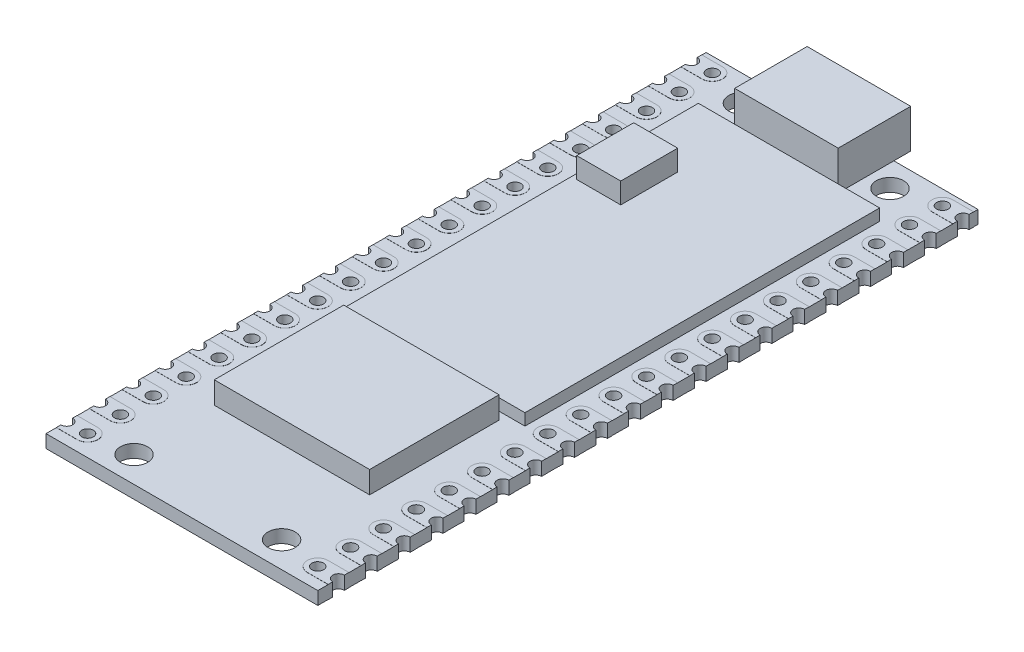
SolidWorks part; units mm, degrees
ref_plane "Front Plane" through (0, 0, 0) normal (0, 0, 1) x (1, 0, 0)
ref_plane "Top Plane" through (0, 0, 0) normal (0, 1, 0) x (1, 0, 0)
ref_plane "Right Plane" through (0, 0, 0) normal (1, 0, 0) x (0, 0, -1)
sketch "Sketch1" plane through (0, 0, 0) normal (0, 1, 0) x (1, 0, 0)
  line L0 (0, 0) -> (0, -51) construction
  line L1 (-10.5, 0) -> (10.5, 0)
  line L2 (-10.5, 0) -> (-10.5, -0.69)
  line L3 (-10.5, -51) -> (10.5, -51)
  line L4 (10.5, 0) -> (10.5, -0.69)
  line L5 (0, -25.5) -> (-10.5, -25.5) construction
  line L6 (-10.5, -48.95) -> (-8.89, -48.95) construction
  line L7 (-10.5, -49.85) -> (-10.5, -51)
  line L8 (10.5, -49.85) -> (10.5, -51)
  line L9 (-10.5, -47.31) -> (-10.5, -48.95)
  line L10 (-10.5, -44.77) -> (-10.5, -46.41)
  line L11 (-10.5, -42.23) -> (-10.5, -43.87)
  line L12 (-10.5, -39.69) -> (-10.5, -41.33)
  line L13 (-10.5, -37.15) -> (-10.5, -38.79)
  line L14 (-10.5, -34.61) -> (-10.5, -36.25)
  line L15 (-10.5, -32.07) -> (-10.5, -33.71)
  line L16 (-10.5, -29.53) -> (-10.5, -31.17)
  line L17 (-10.5, -26.99) -> (-10.5, -28.63)
  line L18 (-10.5, -24.45) -> (-10.5, -26.09)
  line L19 (-10.5, -21.91) -> (-10.5, -23.55)
  line L20 (-10.5, -19.37) -> (-10.5, -21.01)
  line L21 (-10.5, -16.83) -> (-10.5, -18.47)
  line L22 (-10.5, -14.29) -> (-10.5, -15.93)
  line L23 (-10.5, -11.75) -> (-10.5, -13.39)
  line L24 (-10.5, -9.21) -> (-10.5, -10.85)
  line L25 (-10.5, -6.67) -> (-10.5, -8.31)
  line L26 (-10.5, -4.13) -> (-10.5, -5.77)
  line L27 (-10.5, -1.59) -> (-10.5, -3.23)
  line L28 (10.5, -1.59) -> (10.5, -3.23)
  line L29 (10.5, -4.13) -> (10.5, -5.77)
  line L30 (10.5, -6.67) -> (10.5, -8.31)
  line L31 (10.5, -9.21) -> (10.5, -10.85)
  line L32 (10.5, -11.75) -> (10.5, -13.39)
  line L33 (10.5, -14.29) -> (10.5, -15.93)
  line L34 (10.5, -16.83) -> (10.5, -18.47)
  line L35 (10.5, -47.31) -> (10.5, -48.95)
  line L36 (10.5, -44.77) -> (10.5, -46.41)
  line L37 (10.5, -42.23) -> (10.5, -43.87)
  line L38 (10.5, -39.69) -> (10.5, -41.33)
  line L39 (10.5, -37.15) -> (10.5, -38.79)
  line L40 (10.5, -34.61) -> (10.5, -36.25)
  line L41 (10.5, -32.07) -> (10.5, -33.71)
  line L42 (10.5, -29.53) -> (10.5, -31.17)
  line L43 (10.5, -19.37) -> (10.5, -21.01)
  line L44 (10.5, -21.91) -> (10.5, -23.55)
  line L45 (10.5, -24.45) -> (10.5, -26.09)
  line L46 (10.5, -26.99) -> (10.5, -28.63)
  circle A0 centre (-5.7, -2) radius 1.05
  circle A1 centre (5.7, -2) radius 1.05
  circle A4 centre (-8.89, -49.4) radius 0.45
  arc A5 (-10.5, -49.85) -> (-10.5, -48.95) centre (-10.5, -49.4) ccw
  circle A6 centre (5.7, -49) radius 1.05
  circle A7 centre (-5.7, -49) radius 1.05
  arc A8 (10.5, -49.85) -> (10.5, -48.95) centre (10.5, -49.4) cw
  circle A9 centre (8.89, -49.4) radius 0.45
  arc A10 (-10.5, -47.31) -> (-10.5, -46.41) centre (-10.5, -46.86) ccw
  circle A11 centre (-8.89, -46.86) radius 0.45
  circle A12 centre (8.89, -46.86) radius 0.45
  arc A13 (10.5, -47.31) -> (10.5, -46.41) centre (10.5, -46.86) cw
  arc A14 (-10.5, -44.77) -> (-10.5, -43.87) centre (-10.5, -44.32) ccw
  circle A15 centre (-8.89, -44.32) radius 0.45
  circle A16 centre (8.89, -44.32) radius 0.45
  arc A17 (10.5, -44.77) -> (10.5, -43.87) centre (10.5, -44.32) cw
  arc A18 (-10.5, -42.23) -> (-10.5, -41.33) centre (-10.5, -41.78) ccw
  circle A19 centre (-8.89, -41.78) radius 0.45
  circle A20 centre (8.89, -41.78) radius 0.45
  arc A21 (10.5, -42.23) -> (10.5, -41.33) centre (10.5, -41.78) cw
  arc A22 (-10.5, -39.69) -> (-10.5, -38.79) centre (-10.5, -39.24) ccw
  circle A23 centre (-8.89, -39.24) radius 0.45
  circle A24 centre (8.89, -39.24) radius 0.45
  arc A25 (10.5, -39.69) -> (10.5, -38.79) centre (10.5, -39.24) cw
  arc A26 (-10.5, -37.15) -> (-10.5, -36.25) centre (-10.5, -36.7) ccw
  circle A27 centre (-8.89, -36.7) radius 0.45
  circle A28 centre (8.89, -36.7) radius 0.45
  arc A29 (10.5, -37.15) -> (10.5, -36.25) centre (10.5, -36.7) cw
  arc A30 (-10.5, -34.61) -> (-10.5, -33.71) centre (-10.5, -34.16) ccw
  circle A31 centre (-8.89, -34.16) radius 0.45
  circle A32 centre (8.89, -34.16) radius 0.45
  arc A33 (10.5, -34.61) -> (10.5, -33.71) centre (10.5, -34.16) cw
  arc A34 (-10.5, -32.07) -> (-10.5, -31.17) centre (-10.5, -31.62) ccw
  circle A35 centre (-8.89, -31.62) radius 0.45
  circle A36 centre (8.89, -31.62) radius 0.45
  arc A37 (10.5, -32.07) -> (10.5, -31.17) centre (10.5, -31.62) cw
  arc A38 (-10.5, -29.53) -> (-10.5, -28.63) centre (-10.5, -29.08) ccw
  circle A39 centre (-8.89, -29.08) radius 0.45
  circle A40 centre (8.89, -29.08) radius 0.45
  arc A41 (10.5, -29.53) -> (10.5, -28.63) centre (10.5, -29.08) cw
  arc A42 (-10.5, -26.99) -> (-10.5, -26.09) centre (-10.5, -26.54) ccw
  circle A43 centre (-8.89, -26.54) radius 0.45
  circle A44 centre (8.89, -26.54) radius 0.45
  arc A45 (10.5, -26.99) -> (10.5, -26.09) centre (10.5, -26.54) cw
  arc A46 (-10.5, -24.45) -> (-10.5, -23.55) centre (-10.5, -24) ccw
  circle A47 centre (-8.89, -24) radius 0.45
  circle A48 centre (8.89, -24) radius 0.45
  arc A49 (10.5, -24.45) -> (10.5, -23.55) centre (10.5, -24) cw
  arc A50 (-10.5, -21.91) -> (-10.5, -21.01) centre (-10.5, -21.46) ccw
  circle A51 centre (-8.89, -21.46) radius 0.45
  circle A52 centre (8.89, -21.46) radius 0.45
  arc A53 (10.5, -21.91) -> (10.5, -21.01) centre (10.5, -21.46) cw
  arc A54 (-10.5, -19.37) -> (-10.5, -18.47) centre (-10.5, -18.92) ccw
  circle A55 centre (-8.89, -18.92) radius 0.45
  circle A56 centre (8.89, -18.92) radius 0.45
  arc A57 (10.5, -19.37) -> (10.5, -18.47) centre (10.5, -18.92) cw
  arc A58 (-10.5, -16.83) -> (-10.5, -15.93) centre (-10.5, -16.38) ccw
  circle A59 centre (-8.89, -16.38) radius 0.45
  circle A60 centre (8.89, -16.38) radius 0.45
  arc A61 (10.5, -16.83) -> (10.5, -15.93) centre (10.5, -16.38) cw
  arc A62 (-10.5, -14.29) -> (-10.5, -13.39) centre (-10.5, -13.84) ccw
  circle A63 centre (-8.89, -13.84) radius 0.45
  circle A64 centre (8.89, -13.84) radius 0.45
  arc A65 (10.5, -14.29) -> (10.5, -13.39) centre (10.5, -13.84) cw
  arc A66 (-10.5, -11.75) -> (-10.5, -10.85) centre (-10.5, -11.3) ccw
  circle A67 centre (-8.89, -11.3) radius 0.45
  circle A68 centre (8.89, -11.3) radius 0.45
  arc A69 (10.5, -11.75) -> (10.5, -10.85) centre (10.5, -11.3) cw
  arc A70 (-10.5, -9.21) -> (-10.5, -8.31) centre (-10.5, -8.76) ccw
  circle A71 centre (-8.89, -8.76) radius 0.45
  circle A72 centre (8.89, -8.76) radius 0.45
  arc A73 (10.5, -9.21) -> (10.5, -8.31) centre (10.5, -8.76) cw
  arc A74 (-10.5, -6.67) -> (-10.5, -5.77) centre (-10.5, -6.22) ccw
  circle A75 centre (-8.89, -6.22) radius 0.45
  circle A76 centre (8.89, -6.22) radius 0.45
  arc A77 (10.5, -6.67) -> (10.5, -5.77) centre (10.5, -6.22) cw
  arc A78 (-10.5, -4.13) -> (-10.5, -3.23) centre (-10.5, -3.68) ccw
  circle A79 centre (-8.89, -3.68) radius 0.45
  circle A80 centre (8.89, -3.68) radius 0.45
  arc A81 (10.5, -4.13) -> (10.5, -3.23) centre (10.5, -3.68) cw
  arc A82 (-10.5, -1.59) -> (-10.5, -0.69) centre (-10.5, -1.14) ccw
  circle A83 centre (-8.89, -1.14) radius 0.45
  circle A84 centre (8.89, -1.14) radius 0.45
  arc A85 (10.5, -1.59) -> (10.5, -0.69) centre (10.5, -1.14) cw
other "Pen Sketch1" parameters "D3"=3.5614, "D8"=2.0664, "D1"=79.4088, "D2"=21, "D4"=15.5245, "D5"=11.4, "D6"=25.5, "D7"=1.5119, "D10"=2.54, "D9"=20
extrude "Boss-Extrude1" add sketch "Sketch1" along normal blind 1
sketch "Sketch2" plane through (0, 1, 0) normal (0, 1, 0) x (1, 0, 0)
  line L0 (0, -4.3) -> (0, 0) construction
  line L1 (-4, 1.3) -> (4, 1.3)
  line L2 (-4, 1.3) -> (-4, -4.3)
  line L3 (-4, -4.3) -> (4, -4.3)
  line L4 (4, 1.3) -> (4, -4.3)
  line L5 (10.5, 0) -> (-10.5, 0) construction
  dimension "D1" = 8
  dimension "D2" = 5.6
  dimension "D3" = 4.3
extrude "Boss-Extrude2" add sketch "Sketch2" along normal blind 3
sketch "Sketch3" plane through (0, 1, 0) normal (0, 1, 0) x (1, 0, 0)
  line L0 (-8.89, -48.6) -> (-10.5, -48.6)
  line L1 (-10.5, -47.31) -> (-10.5, -48.95) construction
  line L2 (-10.5, -48.6) -> (-10.5, -48.95)
  line L4 (-10.5, -49.85) -> (-10.5, -50.2)
  line L5 (-10.5, -49.85) -> (-10.5, -51) construction
  line L6 (-10.5, -50.2) -> (-8.89, -50.2)
  line L7 (0, 0) -> (0, -51) construction
  line L8 (-10.5, -51) -> (10.5, -51) construction
  line L9 (10.5, -50.2) -> (8.89, -50.2)
  line L10 (10.5, -49.85) -> (10.5, -50.2)
  line L11 (10.5, -48.6) -> (10.5, -48.95)
  line L12 (8.89, -48.6) -> (10.5, -48.6)
  line L13 (-8.89, -46.06) -> (-10.5, -46.06)
  line L14 (-10.5, -46.06) -> (-10.5, -46.41)
  line L15 (-10.5, -47.31) -> (-10.5, -47.66)
  line L16 (-10.5, -47.66) -> (-8.89, -47.66)
  line L17 (10.5, -47.66) -> (8.89, -47.66)
  line L18 (10.5, -47.31) -> (10.5, -47.66)
  line L19 (10.5, -46.06) -> (10.5, -46.41)
  line L20 (8.89, -46.06) -> (10.5, -46.06)
  line L21 (-8.89, -43.52) -> (-10.5, -43.52)
  line L22 (-10.5, -43.52) -> (-10.5, -43.87)
  line L23 (-10.5, -44.77) -> (-10.5, -45.12)
  line L24 (-10.5, -45.12) -> (-8.89, -45.12)
  line L25 (10.5, -45.12) -> (8.89, -45.12)
  line L26 (10.5, -44.77) -> (10.5, -45.12)
  line L27 (10.5, -43.52) -> (10.5, -43.87)
  line L28 (8.89, -43.52) -> (10.5, -43.52)
  line L29 (-8.89, -40.98) -> (-10.5, -40.98)
  line L30 (-10.5, -40.98) -> (-10.5, -41.33)
  line L31 (-10.5, -42.23) -> (-10.5, -42.58)
  line L32 (-10.5, -42.58) -> (-8.89, -42.58)
  line L33 (10.5, -42.58) -> (8.89, -42.58)
  line L34 (10.5, -42.23) -> (10.5, -42.58)
  line L35 (10.5, -40.98) -> (10.5, -41.33)
  line L36 (8.89, -40.98) -> (10.5, -40.98)
  line L37 (-8.89, -38.44) -> (-10.5, -38.44)
  line L38 (-10.5, -38.44) -> (-10.5, -38.79)
  line L39 (-10.5, -39.69) -> (-10.5, -40.04)
  line L40 (-10.5, -40.04) -> (-8.89, -40.04)
  line L41 (10.5, -40.04) -> (8.89, -40.04)
  line L42 (10.5, -39.69) -> (10.5, -40.04)
  line L43 (10.5, -38.44) -> (10.5, -38.79)
  line L44 (8.89, -38.44) -> (10.5, -38.44)
  line L45 (-8.89, -35.9) -> (-10.5, -35.9)
  line L46 (-10.5, -35.9) -> (-10.5, -36.25)
  line L47 (-10.5, -37.15) -> (-10.5, -37.5)
  line L48 (-10.5, -37.5) -> (-8.89, -37.5)
  line L49 (10.5, -37.5) -> (8.89, -37.5)
  line L50 (10.5, -37.15) -> (10.5, -37.5)
  line L51 (10.5, -35.9) -> (10.5, -36.25)
  line L52 (8.89, -35.9) -> (10.5, -35.9)
  line L53 (-8.89, -33.36) -> (-10.5, -33.36)
  line L54 (-10.5, -33.36) -> (-10.5, -33.71)
  line L55 (-10.5, -34.61) -> (-10.5, -34.96)
  line L56 (-10.5, -34.96) -> (-8.89, -34.96)
  line L57 (10.5, -34.96) -> (8.89, -34.96)
  line L58 (10.5, -34.61) -> (10.5, -34.96)
  line L59 (10.5, -33.36) -> (10.5, -33.71)
  line L60 (8.89, -33.36) -> (10.5, -33.36)
  line L61 (-8.89, -30.82) -> (-10.5, -30.82)
  line L62 (-10.5, -30.82) -> (-10.5, -31.17)
  line L63 (-10.5, -32.07) -> (-10.5, -32.42)
  line L64 (-10.5, -32.42) -> (-8.89, -32.42)
  line L65 (10.5, -32.42) -> (8.89, -32.42)
  line L66 (10.5, -32.07) -> (10.5, -32.42)
  line L67 (10.5, -30.82) -> (10.5, -31.17)
  line L68 (8.89, -30.82) -> (10.5, -30.82)
  line L69 (-8.89, -28.28) -> (-10.5, -28.28)
  line L70 (-10.5, -28.28) -> (-10.5, -28.63)
  line L71 (-10.5, -29.53) -> (-10.5, -29.88)
  line L72 (-10.5, -29.88) -> (-8.89, -29.88)
  line L73 (10.5, -29.88) -> (8.89, -29.88)
  line L74 (10.5, -29.53) -> (10.5, -29.88)
  line L75 (10.5, -28.28) -> (10.5, -28.63)
  line L76 (8.89, -28.28) -> (10.5, -28.28)
  line L77 (-8.89, -25.74) -> (-10.5, -25.74)
  line L78 (-10.5, -25.74) -> (-10.5, -26.09)
  line L79 (-10.5, -26.99) -> (-10.5, -27.34)
  line L80 (-10.5, -27.34) -> (-8.89, -27.34)
  line L81 (10.5, -27.34) -> (8.89, -27.34)
  line L82 (10.5, -26.99) -> (10.5, -27.34)
  line L83 (10.5, -25.74) -> (10.5, -26.09)
  line L84 (8.89, -25.74) -> (10.5, -25.74)
  line L85 (-8.89, -23.2) -> (-10.5, -23.2)
  line L86 (-10.5, -23.2) -> (-10.5, -23.55)
  line L87 (-10.5, -24.45) -> (-10.5, -24.8)
  line L88 (-10.5, -24.8) -> (-8.89, -24.8)
  line L89 (10.5, -24.8) -> (8.89, -24.8)
  line L90 (10.5, -24.45) -> (10.5, -24.8)
  line L91 (10.5, -23.2) -> (10.5, -23.55)
  line L92 (8.89, -23.2) -> (10.5, -23.2)
  line L93 (-8.89, -20.66) -> (-10.5, -20.66)
  line L94 (-10.5, -20.66) -> (-10.5, -21.01)
  line L95 (-10.5, -21.91) -> (-10.5, -22.26)
  line L96 (-10.5, -22.26) -> (-8.89, -22.26)
  line L97 (10.5, -22.26) -> (8.89, -22.26)
  line L98 (10.5, -21.91) -> (10.5, -22.26)
  line L99 (10.5, -20.66) -> (10.5, -21.01)
  line L100 (8.89, -20.66) -> (10.5, -20.66)
  line L101 (-8.89, -18.12) -> (-10.5, -18.12)
  line L102 (-10.5, -18.12) -> (-10.5, -18.47)
  line L103 (-10.5, -19.37) -> (-10.5, -19.72)
  line L104 (-10.5, -19.72) -> (-8.89, -19.72)
  line L105 (10.5, -19.72) -> (8.89, -19.72)
  line L106 (10.5, -19.37) -> (10.5, -19.72)
  line L107 (10.5, -18.12) -> (10.5, -18.47)
  line L108 (8.89, -18.12) -> (10.5, -18.12)
  line L109 (-8.89, -15.58) -> (-10.5, -15.58)
  line L110 (-10.5, -15.58) -> (-10.5, -15.93)
  line L111 (-10.5, -16.83) -> (-10.5, -17.18)
  line L112 (-10.5, -17.18) -> (-8.89, -17.18)
  line L113 (10.5, -17.18) -> (8.89, -17.18)
  line L114 (10.5, -16.83) -> (10.5, -17.18)
  line L115 (10.5, -15.58) -> (10.5, -15.93)
  line L116 (8.89, -15.58) -> (10.5, -15.58)
  line L117 (-8.89, -13.04) -> (-10.5, -13.04)
  line L118 (-10.5, -13.04) -> (-10.5, -13.39)
  line L119 (-10.5, -14.29) -> (-10.5, -14.64)
  line L120 (-10.5, -14.64) -> (-8.89, -14.64)
  line L121 (10.5, -14.64) -> (8.89, -14.64)
  line L122 (10.5, -14.29) -> (10.5, -14.64)
  line L123 (10.5, -13.04) -> (10.5, -13.39)
  line L124 (8.89, -13.04) -> (10.5, -13.04)
  line L125 (-8.89, -10.5) -> (-10.5, -10.5)
  line L126 (-10.5, -10.5) -> (-10.5, -10.85)
  line L127 (-10.5, -11.75) -> (-10.5, -12.1)
  line L128 (-10.5, -12.1) -> (-8.89, -12.1)
  line L129 (10.5, -12.1) -> (8.89, -12.1)
  line L130 (10.5, -11.75) -> (10.5, -12.1)
  line L131 (10.5, -10.5) -> (10.5, -10.85)
  line L132 (8.89, -10.5) -> (10.5, -10.5)
  line L133 (-8.89, -7.96) -> (-10.5, -7.96)
  line L134 (-10.5, -7.96) -> (-10.5, -8.31)
  line L135 (-10.5, -9.21) -> (-10.5, -9.56)
  line L136 (-10.5, -9.56) -> (-8.89, -9.56)
  line L137 (10.5, -9.56) -> (8.89, -9.56)
  line L138 (10.5, -9.21) -> (10.5, -9.56)
  line L139 (10.5, -7.96) -> (10.5, -8.31)
  line L140 (8.89, -7.96) -> (10.5, -7.96)
  line L141 (-8.89, -5.42) -> (-10.5, -5.42)
  line L142 (-10.5, -5.42) -> (-10.5, -5.77)
  line L143 (-10.5, -6.67) -> (-10.5, -7.02)
  line L144 (-10.5, -7.02) -> (-8.89, -7.02)
  line L145 (10.5, -7.02) -> (8.89, -7.02)
  line L146 (10.5, -6.67) -> (10.5, -7.02)
  line L147 (10.5, -5.42) -> (10.5, -5.77)
  line L148 (8.89, -5.42) -> (10.5, -5.42)
  line L149 (-8.89, -2.88) -> (-10.5, -2.88)
  line L150 (-10.5, -2.88) -> (-10.5, -3.23)
  line L151 (-10.5, -4.13) -> (-10.5, -4.48)
  line L152 (-10.5, -4.48) -> (-8.89, -4.48)
  line L153 (10.5, -4.48) -> (8.89, -4.48)
  line L154 (10.5, -4.13) -> (10.5, -4.48)
  line L155 (10.5, -2.88) -> (10.5, -3.23)
  line L156 (8.89, -2.88) -> (10.5, -2.88)
  line L157 (-8.89, -0.34) -> (-10.5, -0.34)
  line L158 (-10.5, -0.34) -> (-10.5, -0.69)
  line L159 (-10.5, -1.59) -> (-10.5, -1.94)
  line L160 (-10.5, -1.94) -> (-8.89, -1.94)
  line L161 (10.5, -1.94) -> (8.89, -1.94)
  line L162 (10.5, -1.59) -> (10.5, -1.94)
  line L163 (10.5, -0.34) -> (10.5, -0.69)
  line L164 (8.89, -0.34) -> (10.5, -0.34)
  arc A0 (-8.89, -50.2) -> (-8.89, -48.6) centre (-8.89, -49.4) ccw
  arc A1 (-10.5, -49.85) -> (-10.5, -48.95) centre (-10.5, -49.4) ccw
  circle A2 centre (-8.89, -49.4) radius 0.45
  circle A3 centre (-8.89, -49.4) radius 0.45 construction
  arc A4 (-10.5, -49.85) -> (-10.5, -48.95) centre (-10.5, -49.4) ccw construction
  circle A5 centre (8.89, -49.4) radius 0.45
  arc A6 (10.5, -49.85) -> (10.5, -48.95) centre (10.5, -49.4) cw
  arc A7 (8.89, -50.2) -> (8.89, -48.6) centre (8.89, -49.4) cw
  arc A8 (-8.89, -47.66) -> (-8.89, -46.06) centre (-8.89, -46.86) ccw
  arc A9 (-10.5, -47.31) -> (-10.5, -46.41) centre (-10.5, -46.86) ccw
  circle A10 centre (-8.89, -46.86) radius 0.45
  circle A11 centre (8.89, -46.86) radius 0.45
  arc A12 (10.5, -47.31) -> (10.5, -46.41) centre (10.5, -46.86) cw
  arc A13 (8.89, -47.66) -> (8.89, -46.06) centre (8.89, -46.86) cw
  arc A14 (-8.89, -45.12) -> (-8.89, -43.52) centre (-8.89, -44.32) ccw
  arc A15 (-10.5, -44.77) -> (-10.5, -43.87) centre (-10.5, -44.32) ccw
  circle A16 centre (-8.89, -44.32) radius 0.45
  circle A17 centre (8.89, -44.32) radius 0.45
  arc A18 (10.5, -44.77) -> (10.5, -43.87) centre (10.5, -44.32) cw
  arc A19 (8.89, -45.12) -> (8.89, -43.52) centre (8.89, -44.32) cw
  arc A20 (-8.89, -42.58) -> (-8.89, -40.98) centre (-8.89, -41.78) ccw
  arc A21 (-10.5, -42.23) -> (-10.5, -41.33) centre (-10.5, -41.78) ccw
  circle A22 centre (-8.89, -41.78) radius 0.45
  circle A23 centre (8.89, -41.78) radius 0.45
  arc A24 (10.5, -42.23) -> (10.5, -41.33) centre (10.5, -41.78) cw
  arc A25 (8.89, -42.58) -> (8.89, -40.98) centre (8.89, -41.78) cw
  arc A26 (-8.89, -40.04) -> (-8.89, -38.44) centre (-8.89, -39.24) ccw
  arc A27 (-10.5, -39.69) -> (-10.5, -38.79) centre (-10.5, -39.24) ccw
  circle A28 centre (-8.89, -39.24) radius 0.45
  circle A29 centre (8.89, -39.24) radius 0.45
  arc A30 (10.5, -39.69) -> (10.5, -38.79) centre (10.5, -39.24) cw
  arc A31 (8.89, -40.04) -> (8.89, -38.44) centre (8.89, -39.24) cw
  arc A32 (-8.89, -37.5) -> (-8.89, -35.9) centre (-8.89, -36.7) ccw
  arc A33 (-10.5, -37.15) -> (-10.5, -36.25) centre (-10.5, -36.7) ccw
  circle A34 centre (-8.89, -36.7) radius 0.45
  circle A35 centre (8.89, -36.7) radius 0.45
  arc A36 (10.5, -37.15) -> (10.5, -36.25) centre (10.5, -36.7) cw
  arc A37 (8.89, -37.5) -> (8.89, -35.9) centre (8.89, -36.7) cw
  arc A38 (-8.89, -34.96) -> (-8.89, -33.36) centre (-8.89, -34.16) ccw
  arc A39 (-10.5, -34.61) -> (-10.5, -33.71) centre (-10.5, -34.16) ccw
  circle A40 centre (-8.89, -34.16) radius 0.45
  circle A41 centre (8.89, -34.16) radius 0.45
  arc A42 (10.5, -34.61) -> (10.5, -33.71) centre (10.5, -34.16) cw
  arc A43 (8.89, -34.96) -> (8.89, -33.36) centre (8.89, -34.16) cw
  arc A44 (-8.89, -32.42) -> (-8.89, -30.82) centre (-8.89, -31.62) ccw
  arc A45 (-10.5, -32.07) -> (-10.5, -31.17) centre (-10.5, -31.62) ccw
  circle A46 centre (-8.89, -31.62) radius 0.45
  circle A47 centre (8.89, -31.62) radius 0.45
  arc A48 (10.5, -32.07) -> (10.5, -31.17) centre (10.5, -31.62) cw
  arc A49 (8.89, -32.42) -> (8.89, -30.82) centre (8.89, -31.62) cw
  arc A50 (-8.89, -29.88) -> (-8.89, -28.28) centre (-8.89, -29.08) ccw
  arc A51 (-10.5, -29.53) -> (-10.5, -28.63) centre (-10.5, -29.08) ccw
  circle A52 centre (-8.89, -29.08) radius 0.45
  circle A53 centre (8.89, -29.08) radius 0.45
  arc A54 (10.5, -29.53) -> (10.5, -28.63) centre (10.5, -29.08) cw
  arc A55 (8.89, -29.88) -> (8.89, -28.28) centre (8.89, -29.08) cw
  arc A56 (-8.89, -27.34) -> (-8.89, -25.74) centre (-8.89, -26.54) ccw
  arc A57 (-10.5, -26.99) -> (-10.5, -26.09) centre (-10.5, -26.54) ccw
  circle A58 centre (-8.89, -26.54) radius 0.45
  circle A59 centre (8.89, -26.54) radius 0.45
  arc A60 (10.5, -26.99) -> (10.5, -26.09) centre (10.5, -26.54) cw
  arc A61 (8.89, -27.34) -> (8.89, -25.74) centre (8.89, -26.54) cw
  arc A62 (-8.89, -24.8) -> (-8.89, -23.2) centre (-8.89, -24) ccw
  arc A63 (-10.5, -24.45) -> (-10.5, -23.55) centre (-10.5, -24) ccw
  circle A64 centre (-8.89, -24) radius 0.45
  circle A65 centre (8.89, -24) radius 0.45
  arc A66 (10.5, -24.45) -> (10.5, -23.55) centre (10.5, -24) cw
  arc A67 (8.89, -24.8) -> (8.89, -23.2) centre (8.89, -24) cw
  arc A68 (-8.89, -22.26) -> (-8.89, -20.66) centre (-8.89, -21.46) ccw
  arc A69 (-10.5, -21.91) -> (-10.5, -21.01) centre (-10.5, -21.46) ccw
  circle A70 centre (-8.89, -21.46) radius 0.45
  circle A71 centre (8.89, -21.46) radius 0.45
  arc A72 (10.5, -21.91) -> (10.5, -21.01) centre (10.5, -21.46) cw
  arc A73 (8.89, -22.26) -> (8.89, -20.66) centre (8.89, -21.46) cw
  arc A74 (-8.89, -19.72) -> (-8.89, -18.12) centre (-8.89, -18.92) ccw
  arc A75 (-10.5, -19.37) -> (-10.5, -18.47) centre (-10.5, -18.92) ccw
  circle A76 centre (-8.89, -18.92) radius 0.45
  circle A77 centre (8.89, -18.92) radius 0.45
  arc A78 (10.5, -19.37) -> (10.5, -18.47) centre (10.5, -18.92) cw
  arc A79 (8.89, -19.72) -> (8.89, -18.12) centre (8.89, -18.92) cw
  arc A80 (-8.89, -17.18) -> (-8.89, -15.58) centre (-8.89, -16.38) ccw
  arc A81 (-10.5, -16.83) -> (-10.5, -15.93) centre (-10.5, -16.38) ccw
  circle A82 centre (-8.89, -16.38) radius 0.45
  circle A83 centre (8.89, -16.38) radius 0.45
  arc A84 (10.5, -16.83) -> (10.5, -15.93) centre (10.5, -16.38) cw
  arc A85 (8.89, -17.18) -> (8.89, -15.58) centre (8.89, -16.38) cw
  arc A86 (-8.89, -14.64) -> (-8.89, -13.04) centre (-8.89, -13.84) ccw
  arc A87 (-10.5, -14.29) -> (-10.5, -13.39) centre (-10.5, -13.84) ccw
  circle A88 centre (-8.89, -13.84) radius 0.45
  circle A89 centre (8.89, -13.84) radius 0.45
  arc A90 (10.5, -14.29) -> (10.5, -13.39) centre (10.5, -13.84) cw
  arc A91 (8.89, -14.64) -> (8.89, -13.04) centre (8.89, -13.84) cw
  arc A92 (-8.89, -12.1) -> (-8.89, -10.5) centre (-8.89, -11.3) ccw
  arc A93 (-10.5, -11.75) -> (-10.5, -10.85) centre (-10.5, -11.3) ccw
  circle A94 centre (-8.89, -11.3) radius 0.45
  circle A95 centre (8.89, -11.3) radius 0.45
  arc A96 (10.5, -11.75) -> (10.5, -10.85) centre (10.5, -11.3) cw
  arc A97 (8.89, -12.1) -> (8.89, -10.5) centre (8.89, -11.3) cw
  arc A98 (-8.89, -9.56) -> (-8.89, -7.96) centre (-8.89, -8.76) ccw
  arc A99 (-10.5, -9.21) -> (-10.5, -8.31) centre (-10.5, -8.76) ccw
  circle A100 centre (-8.89, -8.76) radius 0.45
  circle A101 centre (8.89, -8.76) radius 0.45
  arc A102 (10.5, -9.21) -> (10.5, -8.31) centre (10.5, -8.76) cw
  arc A103 (8.89, -9.56) -> (8.89, -7.96) centre (8.89, -8.76) cw
  arc A104 (-8.89, -7.02) -> (-8.89, -5.42) centre (-8.89, -6.22) ccw
  arc A105 (-10.5, -6.67) -> (-10.5, -5.77) centre (-10.5, -6.22) ccw
  circle A106 centre (-8.89, -6.22) radius 0.45
  circle A107 centre (8.89, -6.22) radius 0.45
  arc A108 (10.5, -6.67) -> (10.5, -5.77) centre (10.5, -6.22) cw
  arc A109 (8.89, -7.02) -> (8.89, -5.42) centre (8.89, -6.22) cw
  arc A110 (-8.89, -4.48) -> (-8.89, -2.88) centre (-8.89, -3.68) ccw
  arc A111 (-10.5, -4.13) -> (-10.5, -3.23) centre (-10.5, -3.68) ccw
  circle A112 centre (-8.89, -3.68) radius 0.45
  circle A113 centre (8.89, -3.68) radius 0.45
  arc A114 (10.5, -4.13) -> (10.5, -3.23) centre (10.5, -3.68) cw
  arc A115 (8.89, -4.48) -> (8.89, -2.88) centre (8.89, -3.68) cw
  arc A116 (-8.89, -1.94) -> (-8.89, -0.34) centre (-8.89, -1.14) ccw
  arc A117 (-10.5, -1.59) -> (-10.5, -0.69) centre (-10.5, -1.14) ccw
  circle A118 centre (-8.89, -1.14) radius 0.45
  circle A119 centre (8.89, -1.14) radius 0.45
  arc A120 (10.5, -1.59) -> (10.5, -0.69) centre (10.5, -1.14) cw
  arc A121 (8.89, -1.94) -> (8.89, -0.34) centre (8.89, -1.14) cw
  circle A122 centre (-8.89, -1.14) radius 0.45 construction
  dimension "D1" = 1.6
  dimension "D2" = 20
extrude "Boss-Extrude3" add sketch "Sketch3" along normal blind 0.01 and the other way blind 1.01
sketch "Sketch4" plane through (0, 1, 0) normal (0, 1, 0) x (1, 0, 0)
  line L0 (-10.5, -27.34) -> (-10.5, -28.28) construction
  line L1 (-3.5, -22.3) -> (3.5, -22.3) construction
  line L2 (-3.5, -22.3) -> (-3.5, -29.3) construction
  line L3 (-3.5, -29.3) -> (3.5, -29.3) construction
  line L4 (3.5, -22.3) -> (3.5, -29.3) construction
  line L5 (-10.5, -51) -> (10.5, -51) construction
  line L6 (-6.5, -32) -> (7.5, -32)
  line L9 (7.5, -32) -> (7.5, -4.6)
  line L10 (7.5, -4.6) -> (-6.5, -4.6)
  line L11 (-6.5, -4.6) -> (-6.5, -32)
  line L14 (-4, 0) -> (-10.5, 0) construction
  line L15 (10.5, -0.34) -> (10.5, 0) construction
  line L17 (10.5, 0) -> (4, 0) construction
  line L18 (-10.5, 0) -> (-10.5, -0.34) construction
  dimension "D1" = 7
  dimension "D2" = 7
  dimension "D3" = 7
  dimension "D4" = 21.7
  dimension "D5" = 17
  dimension "D6" = 18
  dimension "D7" = 32
  dimension "D8" = 4.6
extrude "Boss-Extrude4" add sketch "Sketch4" along normal blind 0.9
sketch "Sketch5" plane through (0, 1, 0) normal (0, 1, 0) x (1, 0, 0)
  line L0 (-10.5, -14.64) -> (-10.5, -15.58) construction
  line L1 (-6.1, -10) -> (-2.7, -10)
  line L2 (-6.1, -10) -> (-6.1, -14.4)
  line L3 (-6.1, -14.4) -> (-2.7, -14.4)
  line L4 (-2.7, -10) -> (-2.7, -14.4)
  line L5 (-4, 0) -> (-10.5, 0) construction
  dimension "D1" = 3.4
  dimension "D2" = 4.4
  dimension "D3" = 4.4
  dimension "D4" = 10
extrude "Boss-Extrude5" add sketch "Sketch5" along normal blind 2.5
sketch "Sketch6" plane through (0, 1, 0) normal (0, 1, 0) x (1, 0, 0)
  line L0 (-10.5, -51) -> (10.5, -51) construction
  line L1 (-5.9, -32.6) -> (6.1, -32.6)
  line L2 (-5.9, -32.6) -> (-5.9, -42.6)
  line L3 (-5.9, -42.6) -> (6.1, -42.6)
  line L4 (6.1, -32.6) -> (6.1, -42.6)
  line L5 (-10.5, 0) -> (-10.5, -0.34) construction
  dimension "D1" = 12
  dimension "D2" = 10
  dimension "D3" = 8.4
  dimension "D4" = 4.6
extrude "Boss-Extrude6" add sketch "Sketch6" along normal blind 1.7
